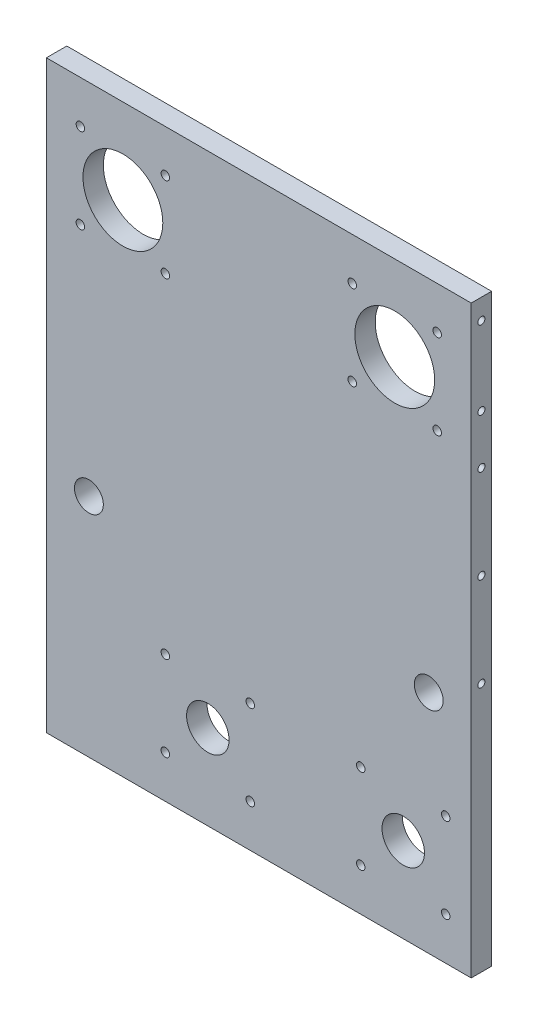
SolidWorks part; units mm, degrees
ref_plane "Front Plane" through (0, 0, 0) normal (0, 0, 1) x (1, 0, 0)
ref_plane "Top Plane" through (0, 0, 0) normal (0, 1, 0) x (1, 0, 0)
ref_plane "Right Plane" through (0, 0, 0) normal (1, 0, 0) x (0, 0, -1)
sketch "Sketch1" plane through (0, 0, 0) normal (0, 0, 1) x (1, 0, 0)
  line L0 (0, 715.3769) -> (0, -220.3769) construction
  line L1 (-125, 294) -> (125, 294)
  line L2 (125, 294) -> (125, -50)
  line L4 (125, -50) -> (-125, -50)
  line L6 (-125, -50) -> (-125, 294)
  circle A0 centre (-80, 244) radius 23.5
  circle A1 centre (80, 244) radius 23.5
  circle A2 centre (-100, 83) radius 8.5
  circle A4 centre (100, 83) radius 8.5
  circle A6 centre (-30, 0) radius 12.5
  circle A9 centre (85, 0) radius 12.5
  dimension "D9" = 47
  dimension "D5" = 17
  dimension "D10" = 344
  dimension "D11" = 25
  dimension "D2" = 211
  dimension "D7" = 25
  dimension "D14" = 40
  dimension "D1" = 250
  dimension "D3" = 160
  dimension "D4" = 200
  dimension "D6" = 50
  dimension "D8" = 294
  dimension "D13" = 50
extrude "Boss-Extrude1" add sketch "Sketch1" along normal blind 12
sketch "Sketch2" plane through (0, 0, 0) normal (0, 0, -1) x (-1, 0, 0)
  circle A0 centre (-80, 244) radius 23.5
  circle A1 centre (80, 244) radius 23.5
  circle A2 centre (-85, 0) radius 12.5
  circle A3 centre (30, 0) radius 12.5
  circle A4 centre (30, 0) radius 12.5 construction
  circle A5 centre (-85, 0) radius 12.5 construction
  circle A6 centre (-80, 244) radius 23.5 construction
  circle A7 centre (80, 244) radius 23.5 construction
  dimension "D5" = 47
  dimension "D1" = 244
  dimension "D2" = 50
  dimension "D3" = 160
  dimension "D4" = 165
sketch "Sketch6" plane through (-125, 0, 0) normal (-1, 0, 0) x (0, 0, 1)
  line L0 (12, 294) -> (0, 294) construction
  point P0 (6, 282)
  point P1 (6, 236)
  dimension "D1" = 6
  dimension "D2" = 12
  dimension "D3" = 58
hole_wizard "Tap Drill for M5 Tap1" positions "Sketch3" profile "Sketch5" hole size "M5" standard "ISO"
sketch "Sketch3" plane through (-125, 0, 0) normal (-1, 0, 0) x (0, 0, 1)
  line L0 (12, 294) -> (12, -50) construction
  line L2 (12, 294) -> (0, 294) construction
  point P0 (6, 282)
  point P9 (6, 282)
  point P11 (6, 236)
  dimension "D1" = 6
  dimension "D2" = 12
sketch "Sketch5" plane through (-125, 282, 6) normal (0, 1, 0) x (0, 0, 1)
  line L0 (0, 0) -> (0, 16.2618)
  line L1 (0, 16.2618) -> (2.1, 15)
  line L2 (2.1, 15) -> (2.1, 0)
  line L5 (2.1, 0) -> (0, 0)
  line L10 (0, 16.2618) -> (-2.1, 15) construction
  line L11 (0, -6.35) -> (0, 107.95) construction
  dimension "Hole Dia." = 4.2
  dimension "Hole Depth" = 15
  dimension "Drill Angle" = 118
mirror "Mirror1" about plane through (0, 0, 0) normal (1, 0, 0) of "Tap Drill for M5 Tap1"
sketch "Sketch7" plane through (0, 0, 12) normal (0, 0, 1) x (1, 0, 0)
  line L0 (-80, 283.5963) -> (-80, 202.5134) construction
  line L1 (-127.2468, 244) -> (-34.1258, 244) construction
  line L2 (80, 283.5963) -> (80, 202.5134) construction
  line L3 (32.7532, 244) -> (125.8742, 244) construction
  line L4 (-30, 29.0045) -> (-30, -52.0784) construction
  line L5 (-74.4956, 0) -> (18.6254, 0) construction
  line L6 (85, 33.2354) -> (85, -47.8475) construction
  line L7 (93.0252, 0) -> (186.1462, 0) construction
  circle A1 centre (-80, 244) radius 23.5 construction
  circle A2 centre (80, 244) radius 23.5 construction
  circle A3 centre (-30, 0) radius 12.5 construction
  circle A4 centre (85, 0) radius 12.5 construction
  point P4 (-105, 269)
  point P5 (-55, 269)
  point P6 (-55, 219)
  point P7 (-105, 219)
  point P10 (-80, 244)
  point P15 (55, 269)
  point P16 (105, 269)
  point P17 (105, 219)
  point P18 (55, 219)
  point P19 (80, 244)
  point P27 (-55, 25)
  point P28 (-5, 25)
  point P29 (-5, -25)
  point P30 (-55, -25)
  point P31 (-30, 0)
  point P37 (60, 25)
  point P38 (110, 25)
  point P39 (110, -25)
  point P41 (60, -25)
  point P42 (85, 0)
  dimension "D1" = 50
  dimension "D2" = 50
  dimension "D3" = 50
  dimension "D4" = 50
  dimension "D5" = 50
  dimension "D6" = 50
  dimension "D7" = 50
  dimension "D8" = 50
hole_wizard "Tap Drill for M6 Tap1" positions "Sketch8" profile "Sketch9" hole size "M6" standard "ISO" end condition through all
sketch "Sketch8" plane through (0, 0, 12) normal (0, 0, 1) x (1, 0, 0)
  point P0 (-105, 269)
  point P3 (-55, 269)
  point P6 (-55, 219)
  point P9 (-105, 219)
  point P12 (55, 219)
  point P15 (105, 219)
  point P18 (105, 269)
  point P21 (55, 269)
  point P24 (-55, 25)
  point P27 (-5, 25)
  point P30 (-5, -25)
  point P33 (-55, -25)
  point P36 (60, 25)
  point P39 (110, 25)
  point P42 (110, -25)
  point P45 (60, -25)
sketch "Sketch9" plane through (-105, 269, 12) normal (1, 0, 0) x (0, -1, 0)
  line L0 (0, 0) -> (0, 12)
  line L1 (0, 12) -> (2.5, 12)
  line L2 (2.5, 12) -> (2.5, 0)
  line L5 (2.5, 0) -> (0, 0)
  line L11 (0, -6.35) -> (0, 107.95) construction
  dimension "Thru Hole Dia." = 5
  dimension "Thru Hole Depth" = 12
sketch "Sketch10" plane through (0, -50, 0) normal (0, -1, 0) x (1, 0, 0)
  line L0 (144.5293, 6) -> (-144.5293, 6) construction
  line L1 (-125, 0) -> (125, 0) construction
  line L2 (125, 12) -> (125, 0) construction
  line L3 (-125, 12) -> (-125, 0) construction
  point P4 (113, 6)
  point P5 (67, 6)
  point P6 (-67, 6)
  point P7 (-113, 6)
  dimension "D1" = 6
  dimension "D2" = 12
  dimension "D3" = 58
  dimension "D4" = 12
  dimension "D5" = 58
hole_wizard "Tap Drill for M5 Tap2" positions "Sketch14" profile "Sketch15" hole size "M5" standard "ISO"
sketch "Sketch14" plane through (0, -50, 0) normal (0, -1, 0) x (-1, 0, 0)
  point P0 (-113, -6)
  point P3 (-67, -6)
  point P6 (67, -6)
  point P9 (113, -6)
sketch "Sketch15" plane through (113, -50, 6) normal (1, 0, 0) x (0, 0, -1)
  line L0 (0, 0) -> (0, 16.2618)
  line L1 (0, 16.2618) -> (2.1, 15)
  line L2 (2.1, 15) -> (2.1, 0)
  line L5 (2.1, 0) -> (0, 0)
  line L10 (0, 16.2618) -> (-2.1, 15) construction
  line L11 (0, -6.35) -> (0, 107.95) construction
  dimension "Hole Dia." = 4.2
  dimension "Hole Depth" = 15
  dimension "Drill Angle" = 118
sketch "Sketch16" plane through (125, 0, 0) normal (1, 0, 0) x (0, 0, -1)
  line L0 (-6, 134.1353) -> (-6, 224.9071) construction
  line L1 (-12, -50) -> (-12, 294) construction
  line L2 (-12, 294) -> (0, 294) construction
  point P0 (-6, 207)
  point P1 (-6, 97)
  point P8 (-6, 152)
  dimension "D1" = 6
  dimension "D2" = 87
  dimension "D3" = 110
  dimension "D4" = 55
hole_wizard "Tap Drill for M5 Tap3" positions "Sketch17" profile "Sketch19" hole size "M5" standard "ISO"
sketch "Sketch17" plane through (125, 0, 0) normal (1, 0, 0) x (0, 0, -1)
  point P0 (-6, 97)
  point P3 (-6, 152)
  point P6 (-6, 207)
sketch "Sketch19" plane through (125, 97, 6) normal (0, 1, 0) x (0, 0, -1)
  line L0 (0, 0) -> (0, 11.2618)
  line L1 (0, 11.2618) -> (2.1, 10)
  line L2 (2.1, 10) -> (2.1, 0)
  line L5 (2.1, 0) -> (0, 0)
  line L10 (0, 11.2618) -> (-2.1, 10) construction
  line L11 (0, -6.35) -> (0, 107.95) construction
  dimension "Hole Dia." = 4.2
  dimension "Hole Depth" = 10
  dimension "Drill Angle" = 118
mirror "Mirror2" about plane through (0, 0, 0) normal (1, 0, 0) of "Tap Drill for M5 Tap3"
